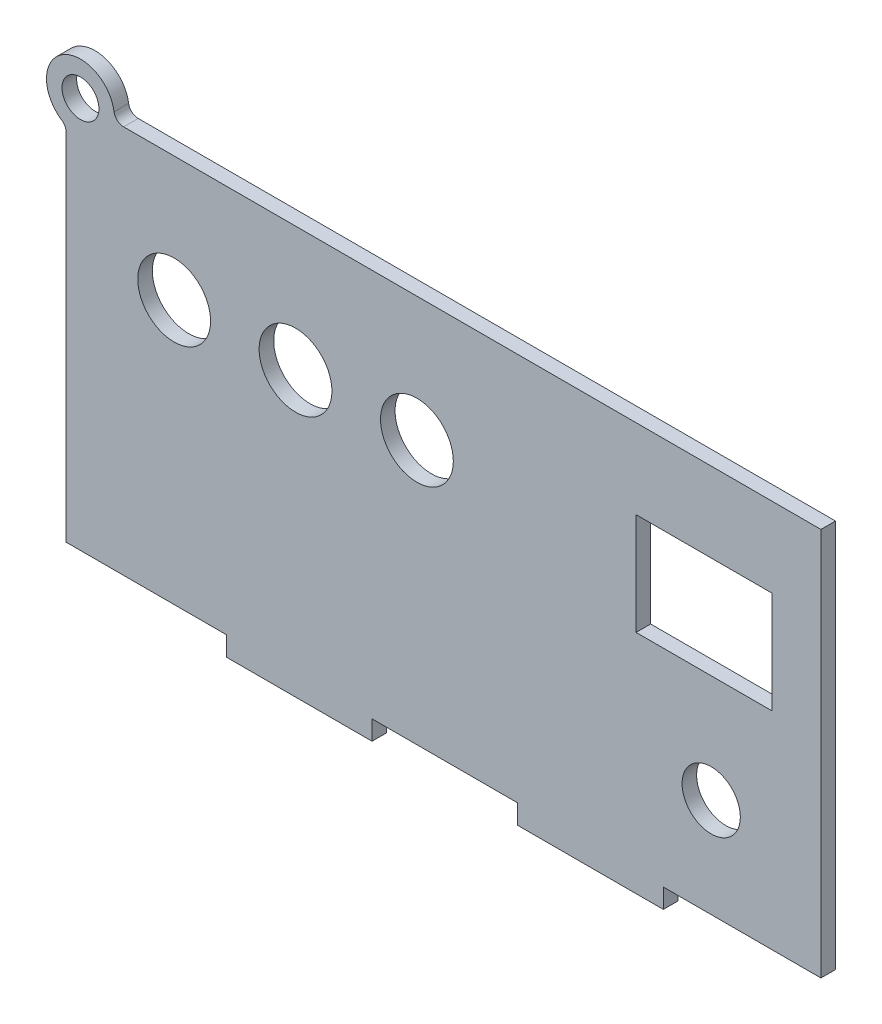
SolidWorks part; units mm, degrees
ref_plane "Front Plane" through (0, 0, 0) normal (0, 0, 1) x (1, 0, 0)
ref_plane "Top Plane" through (0, 0, 0) normal (0, 1, 0) x (1, 0, 0)
ref_plane "Right Plane" through (0, 0, 0) normal (1, 0, 0) x (0, 0, -1)
sketch "Sketch1" plane through (0, 0, 0) normal (0, 0, 1) x (1, 0, 0)
  line L0 (-44.9075, -41.8311) -> (-44.9075, -37.8311)
  line L2 (77.5538, -37.8311) -> (77.5538, 42.1838)
  line L3 (77.5538, 42.1838) -> (-66.0594, 42.1838)
  line L4 (-77.9075, -37.8311) -> (-77.9075, 35.3173)
  line L5 (77.7623, -41.816) -> (-78.4462, 42.1838) construction
  line L6 (77.5538, 42.1838) -> (-78.0896, -42.4752) construction
  line L9 (-77.9075, -37.8311) -> (-74.9075, -37.8311)
  line L11 (-14.9075, -41.8311) -> (-14.9075, -37.8311)
  line L12 (15.0925, -41.8311) -> (15.0925, -37.8311)
  line L13 (45.0925, -41.8311) -> (45.0925, -37.8311)
  line L14 (-14.9075, -37.8311) -> (15.0925, -37.8311)
  line L15 (-74.9075, -37.8311) -> (-44.9075, -37.8311)
  line L17 (-14.9075, -41.8311) -> (-44.9075, -41.8311)
  line L18 (45.0925, -41.8311) -> (15.0925, -41.8311)
  line L19 (45.0925, -37.8311) -> (77.5538, -37.8311)
  line L21 (67.4778, 4.7768) -> (39.4778, 4.7768)
  line L22 (67.4778, 4.7768) -> (67.4778, 25.7768)
  line L23 (67.4778, 25.7768) -> (39.4778, 25.7768)
  line L24 (39.4778, 4.7768) -> (39.4778, 25.7768)
  line L25 (67.4778, 4.7768) -> (39.4778, 25.7768) construction
  line L26 (67.4778, 25.7768) -> (39.4778, 4.7768) construction
  circle A0 centre (-74.9575, 42.8338) radius 3.8
  arc A1 (-68.0367, 43.8838) -> (-78.8075, 36.9876) centre (-74.9575, 42.8338) ccw
  arc A2 (-78.8075, 36.9876) -> (-77.9075, 35.3173) centre (-79.9075, 35.3173) cw
  arc A3 (-68.0367, 43.8838) -> (-66.0594, 42.1838) centre (-66.0594, 44.1838) ccw
  circle A4 centre (-55.6639, 16.4893) radius 7.5
  circle A5 centre (-30.6639, 16.4893) radius 7.5
  circle A6 centre (-5.6639, 16.4893) radius 7.5
  circle A7 centre (54.9509, -17.4407) radius 6
  point P0 (0, 0)
  point P25 (53.4778, 15.2768)
  dimension "D7" = 3
  dimension "D4" = 2
  dimension "D5" = 8.8982
  dimension "D8" = 21
  dimension "D1" = 156
  dimension "D2" = 84
  dimension "D3" = 3
  dimension "D6" = 28
extrude "Boss-Extrude1" add sketch "Sketch1" along normal blind 3
